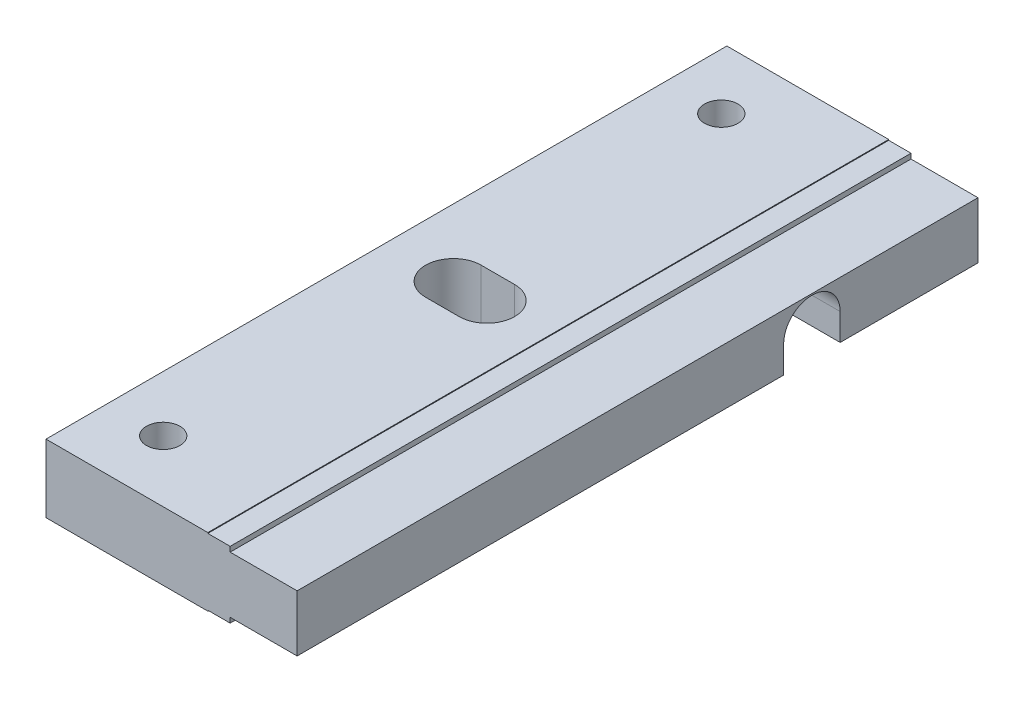
SolidWorks part; units mm, degrees
material "Generic Carbon Fiber"
ref_plane "Front Plane" through (0, 0, 0) normal (0, 0, 1) x (1, 0, 0)
ref_plane "Top Plane" through (0, 0, 0) normal (0, 1, 0) x (1, 0, 0)
ref_plane "Right Plane" through (0, 0, 0) normal (1, 0, 0) x (0, 0, -1)
sketch "Sketch1" plane through (0, 0, 0) normal (1, 0, 0) x (0, 0, -1)
  line L1 (0, -3.05) -> (61, -3.05)
  line L2 (0, -3.05) -> (0, 3.05)
  line L3 (0, 3.05) -> (61, 3.05)
  line L4 (61, -3.05) -> (61, 3.05)
  dimension "D1" = 61
  dimension "D2" = 6.1
extrude "Boss-Extrude1" add sketch "Sketch1" along normal blind 22.5
sketch "Sketch2" plane through (22.5, 0, 0) normal (1, 0, 0) x (0, 0, -1)
  line L0 (0, 3.05) -> (0, -3.05) construction
  line L1 (0, -2.5976) -> (61, -2.5976)
  line L2 (0, -2.5976) -> (0, 2.5976)
  line L3 (0, 2.5976) -> (61, 2.5976)
  line L4 (61, -2.5976) -> (61, 2.5976)
  line L5 (61, -3.05) -> (61, 3.05) construction
  line L7 (30.5, 3.05) -> (30.5, -3.05) construction
  line L8 (61, 3.05) -> (0, 3.05) construction
  line L9 (0, -3.05) -> (61, -3.05) construction
  line L10 (30.5, 0) -> (0, 0) construction
  dimension "D1" = 5.1952
extrude "Cut-Extrude1" cut sketch "Sketch2" against normal blind 6 flip side to cut
sketch "Sketch5" plane through (0, 0, 0) normal (-1, 0, 0) x (0, 0, 1)
  line L0 (-46.119, -0.1278) -> (0, -0.1278) construction
  line L2 (0, 3.05) -> (0, -3.05) construction
  line L3 (0, -3.05) -> (-61, -3.05) construction
  line L4 (-43.5866, -0.1278) -> (-43.5866, -3.05)
  line L5 (-43.5866, -3.05) -> (-48.6514, -3.05)
  line L6 (-48.6514, -3.05) -> (-48.6514, -0.1278)
  line L7 (-61, -3.05) -> (-61, 3.05) construction
  line L8 (-61, 2.5976) -> (0, 2.5976) construction
  arc A0 (-43.5866, -0.1278) -> (-48.6514, -0.1278) centre (-46.119, -0.1278) ccw
  dimension "D1" = 5.0648
  dimension "D2" = 14.881
  dimension "D3" = 2.7254
extrude "Cut-Extrude3" cut sketch "Sketch5" against normal through all
sketch "Sketch6" plane through (0, 3.05, 0) normal (0, 1, 0) x (1, 0, 0)
  line L0 (0, 30.5) -> (22.5, 30.5) construction
  line L2 (22.5, 61) -> (22.5, 0) construction
  line L3 (6, 30.5) -> (9, 30.5) construction
  line L4 (6, 32.9892) -> (9, 32.9892)
  line L5 (6, 28.0108) -> (9, 28.0108)
  line L6 (0, 61) -> (0, 0) construction
  line L7 (0, 61) -> (0, 0) construction
  arc A0 (6, 32.9892) -> (6, 28.0108) centre (6, 30.5) ccw
  arc A1 (9, 28.0108) -> (9, 32.9892) centre (9, 30.5) ccw
  point P8 (7.5, 30.5)
  dimension "D2" = 2.4892
  dimension "D1" = 3
  dimension "D3" = 6
extrude "Cut-Extrude4" cut sketch "Sketch6" against normal through all
sketch "Sketch7" plane through (0, 3.05, 0) normal (0, 1, 0) x (1, 0, 0)
  line L0 (5, 61) -> (5, 0) construction
  line L1 (16.5, 61) -> (0, 61) construction
  line L2 (16.5, 0) -> (0, 0) construction
  line L3 (0, 61) -> (0, 0) construction
  line L4 (0, 30.5) -> (22.5, 30.5) construction
  line L5 (22.5, 61) -> (22.5, 0) construction
  circle A0 centre (5, 55.5) radius 1.5
  circle A1 centre (5, 5.5) radius 1.5
  dimension "D1" = 3
  dimension "D2" = 5
  dimension "D3" = 25
  dimension "D4" = 25
extrude "Cut-Extrude5" cut sketch "Sketch7" against normal through all
sketch "Sketch8" plane through (0, 0, 0) normal (0, 0, 1) x (1, 0, 0)
  line L0 (16.5, -2.5976) -> (16.5, -3.05) construction
  line L1 (14.5, -2.9814) -> (16.5, -2.9814)
  line L2 (14.5, -2.9814) -> (14.5, -3.05)
  line L3 (14.5, -3.05) -> (16.5, -3.05)
  line L4 (16.5, -2.9814) -> (16.5, -3.05)
  line L5 (22.5, 2.5976) -> (22.5, -2.5976) construction
  line L6 (16.5, -2.5976) -> (22.5, -2.5976)
  line L7 (16.5, -2.5976) -> (16.5, -2.529)
  line L8 (16.5, -2.529) -> (22.5, -2.529)
  line L9 (22.5, -2.5976) -> (22.5, -2.529)
  line L11 (22.5, 2.5976) -> (16.5, 2.5976)
  line L12 (22.5, 2.5976) -> (22.5, 2.529)
  line L13 (22.5, 2.529) -> (16.5, 2.529)
  line L14 (16.5, 2.5976) -> (16.5, 2.529)
  line L15 (16.5, 3.05) -> (14.5, 3.05)
  line L16 (16.5, 3.05) -> (16.5, 2.9814)
  line L17 (16.5, 2.9814) -> (14.5, 2.9814)
  line L18 (14.5, 3.05) -> (14.5, 2.9814)
  line L20 (16.5, 3.05) -> (0, 3.05) construction
  line L21 (14.5, -2.9814) -> (14.5, 2.9814) construction
  dimension "D1" = 0.0686
  dimension "D2" = 0.0686
  dimension "D3" = 0.0686
  dimension "D4" = 0.0686
  dimension "D5" = 2
extrude "Cut-Extrude6" cut sketch "Sketch8" against normal through all
